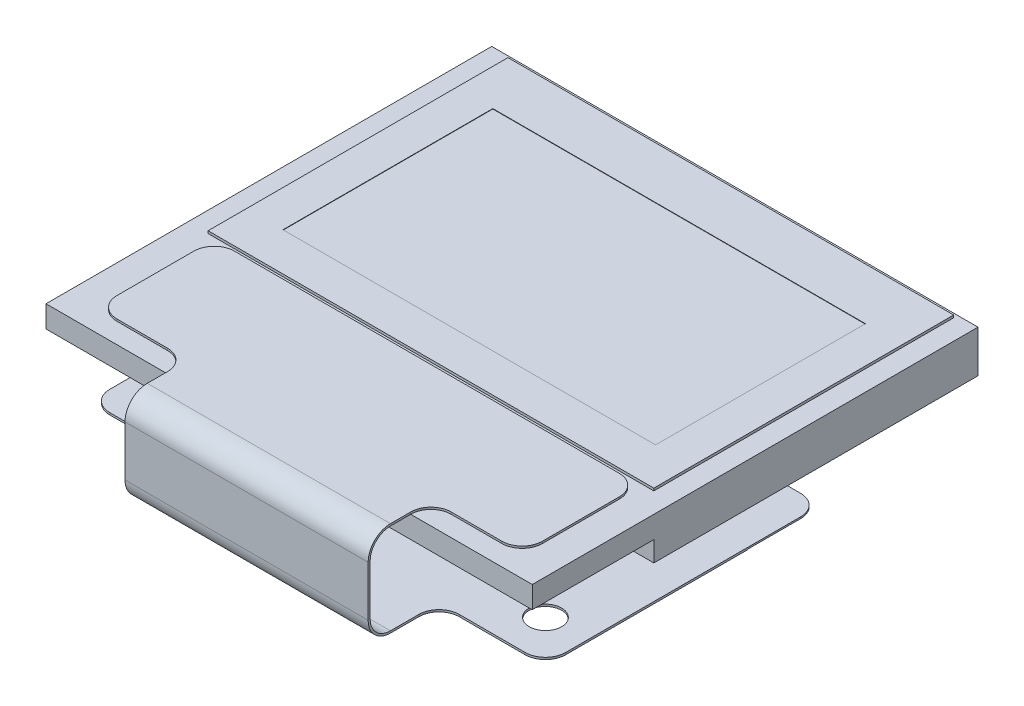
SolidWorks part; units mm, degrees
ref_plane "Front Plane" through (0, 0, 0) normal (0, 0, 1) x (1, 0, 0)
ref_plane "Top Plane" through (0, 0, 0) normal (0, 1, 0) x (1, 0, 0)
ref_plane "Right Plane" through (0, 0, 0) normal (1, 0, 0) x (0, 0, -1)
sketch "Sketch1" plane through (0, 0, 0) normal (0, 1, 0) x (1, 0, 0)
  line L1 (-6, 5.5) -> (6, 5.5)
  line L2 (-6, 5.5) -> (-6, -5.5)
  line L3 (-6, -5.5) -> (6, -5.5)
  line L4 (6, 5.5) -> (6, -5.5)
  line L5 (-6, 5.5) -> (6, -5.5) construction
  line L6 (-6, -5.5) -> (6, 5.5) construction
  point P0 (0, 0)
  dimension "D1" = 12
  dimension "D2" = 11
extrude "Boss-Extrude1" add sketch "Sketch1" along normal blind 1.1
sketch "Sketch2" plane through (0, 1.1, 0) normal (0, 1, 0) x (1, 0, 0)
  line L6 (0, -5.5) -> (0, 5.5) construction
  line L7 (-5.5, 5.4) -> (5.5, 5.4)
  line L8 (-5.5, 5.4) -> (-5.5, -2)
  line L9 (-5.5, -2) -> (5.5, -2)
  line L10 (6, -5.5) -> (6, 5.5)
  line L11 (6, 5.5) -> (-6, 5.5)
  line L12 (-6, 5.5) -> (-6, -5.5)
  line L13 (-6, -5.5) -> (6, -5.5)
  line L14 (6, -5.5) -> (6, 5.5)
  line L15 (6, 5.5) -> (-6, 5.5)
  line L16 (-6, 5.5) -> (-6, -5.5)
  line L17 (-6, -5.5) -> (6, -5.5)
  line L18 (5.5, 5.4) -> (5.5, -2)
  dimension "D1" = 0
  dimension "D2" = 11
  dimension "D3" = 0.1
  dimension "D4" = 7.5
extrude "Cut-Extrude1" cut sketch "Sketch2" against normal blind 0.06
sketch "Sketch3" plane through (0, 1.1, 0) normal (0, 1, 0) x (1, 0, 0)
  line L0 (0, 5.4) -> (0, -2) construction
  line L1 (-4.598, 4.125) -> (4.598, 4.125)
  line L2 (-4.598, 4.125) -> (-4.598, -1.055)
  line L3 (-4.598, -1.055) -> (4.598, -1.055)
  line L4 (4.598, 4.125) -> (4.598, -1.055)
  line L5 (5.5, 5.4) -> (-5.5, 5.4) construction
  line L6 (-5.5, -2) -> (5.5, -2) construction
  line L7 (6, 5.5) -> (-6, 5.5) construction
  dimension "D1" = 9.196
  dimension "D2" = 5.18
  dimension "D3" = 1.375
extrude "Cut-Extrude2" cut sketch "Sketch3" against normal blind 0.01
sketch "Sketch4" plane through (0, 0, 0) normal (0, -1, 0) x (1, 0, 0)
  line L0 (6, 5.5) -> (6, -5.5) construction
  line L1 (-6, 5.5) -> (6, 5.5)
  line L2 (-6, 5.5) -> (-6, 2.5)
  line L3 (-6, 2.5) -> (6, 2.5)
  line L4 (6, 5.5) -> (6, 2.5)
  line L5 (6, -5.5) -> (-6, -5.5) construction
  dimension "D1" = 8
extrude "Cut-Extrude3" cut sketch "Sketch4" against normal blind 0.5
sketch "Sketch5" plane through (0, 1.04, 0) normal (0, 1, 0) x (1, 0, 0)
  line L0 (0, 0) -> (0, -5.5) construction
  line L1 (-4.75, -2.1) -> (4.75, -2.1)
  line L2 (-5.25, -2.6) -> (-5.25, -4.5)
  line L3 (-4.75, -5) -> (-3.5, -5)
  line L4 (5.25, -2.6) -> (5.25, -4.5)
  line L5 (-6, -5.5) -> (6, -5.5) construction
  line L6 (-5.5, -2) -> (5.5, -2) construction
  line L7 (3.5, -5) -> (4.75, -5)
  line L8 (-3, -5) -> (0, -5) construction
  line L9 (-3, -5.5) -> (-3, -6)
  line L10 (-3, -6) -> (3, -6)
  line L11 (3, -5.5) -> (3, -6)
  line L12 (-3, -5) -> (0, -5) construction
  line L13 (0, -5) -> (3, -5) construction
  line L14 (0, -5) -> (3, -5) construction
  arc A0 (3.5, -5) -> (3, -5.5) centre (3.5, -5.5) ccw
  arc A1 (-3.5, -5) -> (-3, -5.5) centre (-3.5, -5.5) cw
  arc A2 (4.75, -2.1) -> (5.25, -2.6) centre (4.75, -2.6) cw
  arc A3 (4.75, -5) -> (5.25, -4.5) centre (4.75, -4.5) ccw
  arc A4 (-5.25, -4.5) -> (-4.75, -5) centre (-4.75, -4.5) ccw
  arc A5 (-4.75, -2.1) -> (-5.25, -2.6) centre (-4.75, -2.6) ccw
  point P26 (5.25, -5)
  point P29 (-5.25, -5)
  dimension "D6" = 0.5
  dimension "D1" = 0.1
  dimension "D2" = 10.5
  dimension "D3" = 0.5
  dimension "D4" = 6
  dimension "D5" = 0.5
extrude "Boss-Extrude2" add sketch "Sketch5" along normal blind 0.05
sketch "Sketch6" plane through (0, 0, 0) normal (1, 0, 0) x (0, 0, -1)
  line L0 (-6, 1.09) -> (-6, 1.04) construction
  line L1 (-6.5, 0.54) -> (-6.5, -0.7)
  line L2 (-2.5, 0) -> (5.5, 0) construction
  line L3 (-6.55, 0.54) -> (-6.55, -0.7)
  line L4 (-6, 1.09) -> (-6, 1.04)
  line L5 (-6, -1.25) -> (2, -1.25)
  line L6 (2, -1.25) -> (2, -1.2)
  line L7 (2, -1.2) -> (-6, -1.2)
  line L8 (-6, 1.09) -> (-5.5, 1.09) construction
  arc A0 (-6, 1.04) -> (-6.5, 0.54) centre (-6, 0.54) ccw
  arc A1 (-6.5, -0.7) -> (-6, -1.2) centre (-6, -0.7) ccw
  arc A2 (-6, 1.09) -> (-6.55, 0.54) centre (-6, 0.54) ccw
  arc A3 (-6.55, -0.7) -> (-6, -1.25) centre (-6, -0.7) ccw
  dimension "D1" = 0.5
  dimension "D2" = 1.2
  dimension "D4" = 2.34
  dimension "D5" = 8
  dimension "D3" = 0.05
extrude "Boss-Extrude3" add sketch "Sketch6" along normal mid plane 6
sketch "Sketch7" plane through (0, -1.25, 0) normal (0, -1, 0) x (1, 0, 0)
  line L0 (0, 0) -> (0, 4.0041) construction
  line L1 (-5.625, -2) -> (5.625, -2)
  line L2 (-5.625, -2) -> (-5.625, 4.8)
  line L3 (-5.625, 4.8) -> (5.625, 4.8)
  line L4 (5.625, -2) -> (5.625, 4.8)
  line L5 (3, -2) -> (-3, -2) construction
  circle A0 centre (-4.625, 3.8) radius 0.4
  circle A1 centre (4.625, 3.8) radius 0.4
  dimension "D4" = 0.8
  dimension "D1" = 11.25
  dimension "D2" = 6.8
  dimension "D3" = 1
  dimension "D5" = 5.8
extrude "Boss-Extrude4" add sketch "Sketch7" against normal up to surface (0.05 mm away) up to face at (0, -1.2, 2)
sketch "Sketch8" plane through (0, -1.25, 0) normal (0, -1, 0) x (1, 0, 0)
  line L0 (5.625, -2) -> (-5.625, -2) construction
  line L1 (-0.15, -2) -> (0.15, -2)
  line L2 (-0.15, -2) -> (-0.15, -0.2)
  line L3 (-0.15, -0.2) -> (0.15, -0.2)
  line L4 (0.15, -2) -> (0.15, -0.2)
  line L5 (0, 6) -> (0, 0) construction
  line L6 (3, 6) -> (-3, 6) construction
  line L7 (0.5, -2) -> (0.5, -0.2)
  line L8 (0.5, -2) -> (0.8, -2)
  line L9 (0.8, -2) -> (0.8, -0.2)
  line L10 (0.5, -0.2) -> (0.8, -0.2)
  line L11 (1.15, -2) -> (1.15, -0.2)
  line L12 (1.15, -2) -> (1.45, -2)
  line L13 (1.45, -2) -> (1.45, -0.2)
  line L14 (1.15, -0.2) -> (1.45, -0.2)
  line L15 (1.8, -2) -> (1.8, -0.2)
  line L16 (1.8, -2) -> (2.1, -2)
  line L17 (2.1, -2) -> (2.1, -0.2)
  line L18 (1.8, -0.2) -> (2.1, -0.2)
  line L19 (2.45, -2) -> (2.45, -0.2)
  line L20 (2.45, -2) -> (2.75, -2)
  line L21 (2.75, -2) -> (2.75, -0.2)
  line L22 (2.45, -0.2) -> (2.75, -0.2)
  line L23 (3.1, -2) -> (3.1, -0.2)
  line L24 (3.1, -2) -> (3.4, -2)
  line L25 (3.4, -2) -> (3.4, -0.2)
  line L26 (3.1, -0.2) -> (3.4, -0.2)
  line L27 (3.75, -2) -> (3.75, -0.2)
  line L28 (3.75, -2) -> (4.05, -2)
  line L29 (4.05, -2) -> (4.05, -0.2)
  line L30 (3.75, -0.2) -> (4.05, -0.2)
  line L31 (4.4, -2) -> (4.4, -0.2)
  line L32 (4.4, -2) -> (4.7, -2)
  line L33 (4.7, -2) -> (4.7, -0.2)
  line L34 (4.4, -0.2) -> (4.7, -0.2)
  line L35 (-4.4, -2) -> (-4.7, -2)
  line L36 (-4.7, -2) -> (-4.7, -0.2)
  line L37 (-4.4, -0.2) -> (-4.7, -0.2)
  line L38 (-4.4, -2) -> (-4.4, -0.2)
  line L39 (-3.75, -2) -> (-4.05, -2)
  line L40 (-4.05, -2) -> (-4.05, -0.2)
  line L41 (-3.75, -0.2) -> (-4.05, -0.2)
  line L42 (-3.75, -2) -> (-3.75, -0.2)
  line L43 (-3.1, -2) -> (-3.4, -2)
  line L44 (-3.4, -2) -> (-3.4, -0.2)
  line L45 (-3.1, -0.2) -> (-3.4, -0.2)
  line L46 (-3.1, -2) -> (-3.1, -0.2)
  line L47 (-2.45, -2) -> (-2.75, -2)
  line L48 (-2.75, -2) -> (-2.75, -0.2)
  line L49 (-2.45, -0.2) -> (-2.75, -0.2)
  line L50 (-2.45, -2) -> (-2.45, -0.2)
  line L51 (-1.8, -2) -> (-2.1, -2)
  line L52 (-2.1, -2) -> (-2.1, -0.2)
  line L53 (-1.8, -0.2) -> (-2.1, -0.2)
  line L54 (-1.8, -2) -> (-1.8, -0.2)
  line L55 (-1.15, -2) -> (-1.45, -2)
  line L56 (-1.45, -2) -> (-1.45, -0.2)
  line L57 (-1.15, -0.2) -> (-1.45, -0.2)
  line L58 (-1.15, -2) -> (-1.15, -0.2)
  line L59 (-0.5, -2) -> (-0.8, -2)
  line L60 (-0.8, -2) -> (-0.8, -0.2)
  line L61 (-0.5, -0.2) -> (-0.8, -0.2)
  line L62 (-0.5, -2) -> (-0.5, -0.2)
  line L63 (5.625, -2) -> (5.625, 4.8) construction
  line L64 (5.05, -2) -> (5.625, -2)
  line L65 (5.05, -2) -> (5.05, -0.2)
  line L66 (5.05, -0.2) -> (5.625, -0.2)
  line L67 (5.625, -2) -> (5.625, -0.2)
  line L68 (-5.625, 4.8) -> (-5.625, -2) construction
  line L69 (-5.05, -2) -> (-5.625, -2)
  line L70 (-5.05, -2) -> (-5.05, -0.2)
  line L71 (-5.05, -0.2) -> (-5.625, -0.2)
  line L72 (-5.625, -2) -> (-5.625, -0.2)
  point P79 (-5.05, -0.2)
  point P80 (5.05, -0.2)
  dimension "D1" = 1.8
  dimension "D2" = 0.3
  dimension "D4" = 0.65
  dimension "D5" = 0.35
  dimension "D6" = 0.35
  dimension "D3" = 8
extrude "Cut-Extrude4" cut sketch "Sketch8" against normal blind 0.01
sketch "Sketch10" plane through (0, -1.25, 0) normal (0, -1, 0) x (1, 0, 0)
  line L0 (5.05, -0.2) -> (5.05, -2) construction
  line L1 (-5.05, -0.2) -> (5.05, -0.2)
  line L2 (-5.05, -0.2) -> (-5.05, -0.25)
  line L3 (-5.05, -0.25) -> (5.05, -0.25)
  line L4 (5.05, -0.2) -> (5.05, -0.25)
  dimension "D1" = 0.05
extrude "Cut-Extrude5" cut sketch "Sketch10" against normal up to surface (0.01 mm away) up to face at (-5.3375, -1.24, -1.1)
fillet "Fillet1" radius 0.5 6 edges at (3, -1.225, 4.8) (-3, -1.225, 4.8) (-5.625, -1.225, 4.8) (5.625, -1.225, 4.8) (5.625, -1.22, -2) (-5.625, -1.22, -2)
